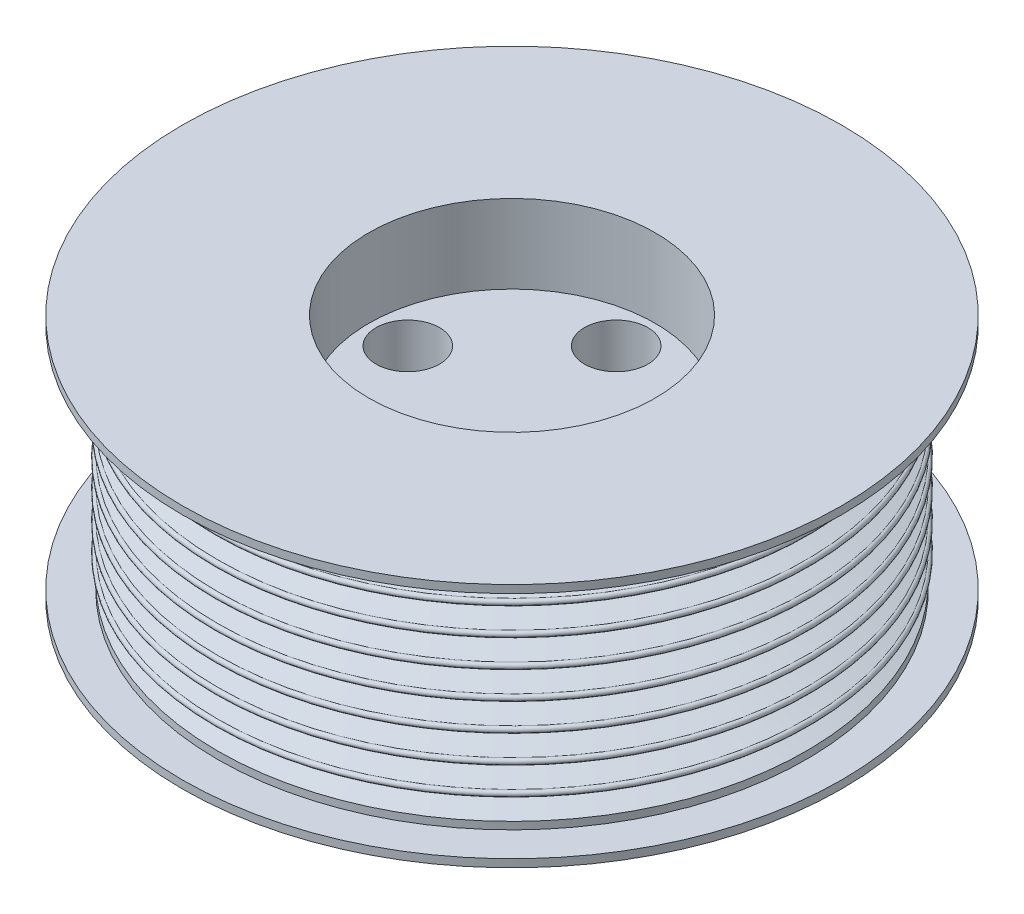
SolidWorks part; units mm, degrees
material "6061-T6 (SS)"
ref_plane "Front Plane" through (0, 0, 0) normal (0, 0, 1) x (1, 0, 0)
ref_plane "Top Plane" through (0, 0, 0) normal (0, 1, 0) x (1, 0, 0)
ref_plane "Right Plane" through (0, 0, 0) normal (1, 0, 0) x (0, 0, -1)
sketch "Sketch1" plane through (0, 0, 0) normal (0, 0, 1) x (1, 0, 0)
  line L0 (38.1, 13.904) -> (38.1, 14.8565)
  line L1 (38.1, -13.904) -> (38.1, -14.8565)
  line L2 (42.672, -15.8725) -> (38.1, -15.8725)
  line L3 (38.1, -13.904) -> (35.2876, -12.8803)
  line L4 (35.2876, -12.8803) -> (35.2876, -12.1183) construction
  line L5 (35.2876, -12.1183) -> (38.1, -11.0947)
  line L6 (38.1, -11.0947) -> (38.1, -10.3327) construction
  line L7 (38.1, -10.3327) -> (35.2876, -9.3091)
  line L8 (35.2876, -9.3091) -> (35.2876, -8.5471) construction
  line L9 (35.2876, -8.5471) -> (38.1, -7.5235)
  line L10 (38.1, -7.5235) -> (38.1, -6.7615) construction
  line L11 (38.1, -6.7615) -> (35.2876, -5.7379)
  line L12 (35.2876, -5.7379) -> (35.2876, -4.9759) construction
  line L13 (35.2876, -4.9759) -> (38.1, -3.9522)
  line L14 (38.1, -3.9522) -> (38.1, -3.1902) construction
  line L15 (38.1, -3.1902) -> (35.2876, -2.1666)
  line L16 (35.2876, -2.1666) -> (35.2876, -1.4046) construction
  line L17 (35.2876, -1.4046) -> (38.1, -0.381)
  line L18 (38.1, -0.381) -> (38.1, 0.381) construction
  line L19 (38.1, 0.381) -> (35.2876, 1.4046)
  line L20 (35.2876, 1.4046) -> (35.2876, 2.1666) construction
  line L21 (35.2876, 2.1666) -> (38.1, 3.1902)
  line L22 (38.1, 3.1902) -> (38.1, 3.9522) construction
  line L23 (38.1, 3.9522) -> (35.2876, 4.9759)
  line L24 (35.2876, 4.9759) -> (35.2876, 5.7379) construction
  line L25 (35.2876, 5.7379) -> (38.1, 6.7615)
  line L26 (38.1, 6.7615) -> (38.1, 7.5235) construction
  line L27 (38.1, 7.5235) -> (35.2876, 8.5471)
  line L28 (35.2876, 8.5471) -> (35.2876, 9.3091) construction
  line L29 (35.2876, 9.3091) -> (38.1, 10.3327)
  line L30 (38.1, 10.3327) -> (38.1, 11.0947) construction
  line L31 (38.1, 11.0947) -> (35.2876, 12.1183)
  line L32 (35.2876, 12.1183) -> (35.2876, 12.8803) construction
  line L33 (35.2876, 12.8803) -> (38.1, 13.904)
  line L34 (38.1, -15.8725) -> (0, -15.8725)
  line L35 (38.1, 15.8725) -> (0, 15.8725)
  line L36 (0, 15.8725) -> (0, -15.8725)
  line L37 (38.1, 10.7137) -> (23.534, 10.7137) construction
  line L38 (38.1, -13.904) -> (38.1, -11.0947) construction
  line L39 (42.672, -15.8725) -> (42.672, -14.8565)
  line L40 (42.672, -14.8565) -> (38.1, -14.8565)
  line L42 (38.1, 15.8725) -> (42.672, 15.8725)
  line L43 (42.672, 15.8725) -> (42.672, 14.8565)
  line L44 (42.672, 14.8565) -> (38.1, 14.8565)
  arc A0 (35.2876, 12.8803) -> (35.2876, 12.1183) centre (35.2876, 12.4993) ccw
  arc A1 (35.2876, 9.3091) -> (35.2876, 8.5471) centre (35.2876, 8.9281) ccw
  arc A2 (35.2876, 5.7379) -> (35.2876, 4.9759) centre (35.2876, 5.3569) ccw
  arc A3 (35.2876, 2.1666) -> (35.2876, 1.4046) centre (35.2876, 1.7856) ccw
  arc A4 (35.2876, -1.4046) -> (35.2876, -2.1666) centre (35.2876, -1.7856) ccw
  arc A5 (35.2876, -4.9759) -> (35.2876, -5.7379) centre (35.2876, -5.3569) ccw
  arc A6 (35.2876, -8.5471) -> (35.2876, -9.3091) centre (35.2876, -8.9281) ccw
  arc A7 (35.2876, -12.1183) -> (35.2876, -12.8803) centre (35.2876, -12.4993) ccw
  arc A8 (38.1, 11.0947) -> (38.1, 10.3327) centre (38.1, 10.7137) cw
  arc A9 (38.1, 7.5235) -> (38.1, 6.7615) centre (38.1, 7.1425) cw
  arc A10 (38.1, 3.1902) -> (38.1, 3.9522) centre (38.1, 3.5712) ccw
  arc A11 (38.1, -0.381) -> (38.1, 0.381) centre (38.1, 0) ccw
  arc A12 (38.1, -3.9522) -> (38.1, -3.1902) centre (38.1, -3.5712) ccw
  arc A13 (38.1, -7.5235) -> (38.1, -6.7615) centre (38.1, -7.1425) ccw
  arc A14 (38.1, -11.0947) -> (38.1, -10.3327) centre (38.1, -10.7137) ccw
  point P1 (0, 0)
  dimension "D9" = 0.9525
  dimension "D5" = 0.381
  dimension "D1" = 20
  dimension "D2" = 20
  dimension "D3" = 3.5712
  dimension "D4" = 38.1
  dimension "D7" = 4.572
  dimension "D8" = 1.016
revolve "Revolve1" add sketch "Sketch1" angle 360 about L36
sketch "Sketch2" plane through (0, 15.8725, 0) normal (0, 1, 0) x (1, 0, 0)
  circle A0 centre (0, 0) radius 18.542
  dimension "D1" = 37.084
extrude "Cut-Extrude1" cut sketch "Sketch2" against normal blind 10.16
sketch "Sketch6" plane through (0, 15.8725, 0) normal (0, 1, 0) x (1, 0, 0)
  circle A0 centre (0, 0) radius 43.5154
  circle A1 centre (0, 0) radius 24.892
  circle A2 centre (0, 0) radius 18.542 construction
  dimension "D1" = 6.35
extrude "Cut-Extrude2" [suppressed] cut sketch "Sketch6" against normal offset from surface (1.27 mm away) 30.48
sketch "Sketch8" plane through (0, -15.8725, 0) normal (0, -1, 0) x (1, 0, 0)
  line L0 (0, 0) -> (0, -13.4874) construction
  dimension "D1" = 13.4874
hole_wizard "5/16 Clearance Hole1" positions "Sketch10" profile "Sketch11" hole size "5/16" standard "Ansi Inch" end condition through all
sketch "Sketch10" plane through (0, -15.8725, 0) normal (0, -1, 0) x (1, 0, 0)
  point P1 (0, -13.4874)
sketch "Sketch11" plane through (0, -15.8725, -13.4874) normal (1, 0, 0) x (0, 0, -1)
  line L0 (0, 0) -> (0, 31.7449)
  line L1 (0, 31.7449) -> (4.1021, 31.7449)
  line L2 (4.1021, 31.7449) -> (4.1021, 0)
  line L5 (4.1021, 0) -> (0, 0)
  line L11 (0, -6.35) -> (0, 107.95) construction
  dimension "Thru Hole Dia." = 8.2042
  dimension "Thru Hole Depth" = 31.7449
pattern_circular "CirPattern1" count 4 over 360 about axis through (0, 0, 0) along (0, 1, 0) of "5/16 Clearance Hole1"
equation "\"D2@Sketch1\" = \"D1@Sketch1\""
